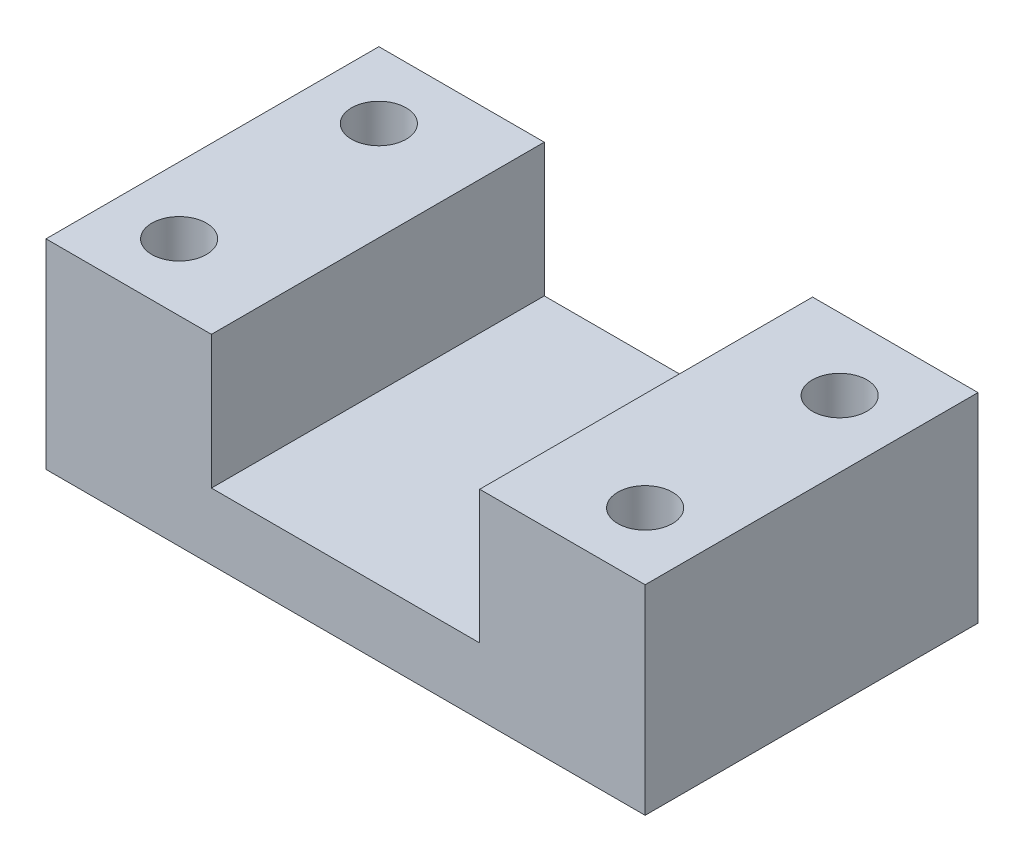
SolidWorks part; units mm, degrees
ref_plane "Спереди" through (0, 0, 0) normal (0, 0, 1) x (1, 0, 0)
ref_plane "Сверху" through (0, 0, 0) normal (0, 1, 0) x (1, 0, 0)
ref_plane "Справа" through (0, 0, 0) normal (1, 0, 0) x (0, 0, -1)
sketch "Sketch1" plane through (0, 0, 0) normal (0, 1, 0) x (1, 0, 0)
  line L1 (45, -25) -> (-45, -25)
  line L2 (45, -25) -> (45, 25)
  line L3 (45, 25) -> (-45, 25)
  line L4 (-45, -25) -> (-45, 25)
  line L5 (45, -25) -> (-45, 25) construction
  line L6 (45, 25) -> (-45, -25) construction
  point P0 (0, 0)
  dimension "D1" = 90
  dimension "D2" = 50
extrude "Boss-Extrude1" add sketch "Sketch1" along normal blind 30
sketch "Sketch2" plane through (0, 0, 25) normal (0, 0, 1) x (1, 0, 0)
  line L0 (-45, 30) -> (45, 30) construction
  line L1 (20.15, 50) -> (-20.15, 50)
  line L2 (20.15, 50) -> (20.15, 10)
  line L3 (20.15, 10) -> (-20.15, 10)
  line L4 (-20.15, 50) -> (-20.15, 10)
  line L5 (20.15, 50) -> (-20.15, 10) construction
  line L6 (20.15, 10) -> (-20.15, 50) construction
  point P0 (0, 30)
  dimension "D1" = 40.3
  dimension "D2" = 40
extrude "Cut-Extrude1" cut sketch "Sketch2" against normal through all
sketch "Sketch3" plane through (0, 0, 0) normal (0, -1, 0) x (1, 0, 0)
  line L1 (-35, -15) -> (35, -15) construction
  line L2 (-35, -15) -> (-35, 15) construction
  line L3 (-35, 15) -> (35, 15) construction
  line L4 (35, -15) -> (35, 15) construction
  line L5 (-35, -15) -> (35, 15) construction
  line L6 (-35, 15) -> (35, -15) construction
  circle A0 centre (-35, 15) radius 4.1
  circle A1 centre (-35, -15) radius 4.1
  circle A2 centre (35, -14.2173) radius 4.1
  circle A3 centre (35, 15) radius 4.1
  point P0 (0, 0)
  point P11 (35, 0)
  dimension "D3" = 8.2
  dimension "D1" = 30
  dimension "D2" = 70
extrude "Cut-Extrude2" cut sketch "Sketch3" against normal through all
sketch "Sketch4" plane through (0, 0, 0) normal (0, -1, 0) x (1, 0, 0)
  circle A0 centre (35, 15) radius 8
  circle A1 centre (35, -14.2173) radius 8
  circle A2 centre (-35, 15) radius 8
  circle A3 centre (-35, -15) radius 8
  dimension "D1" = 16
extrude "Cut-Extrude3" cut sketch "Sketch4" against normal blind 7
